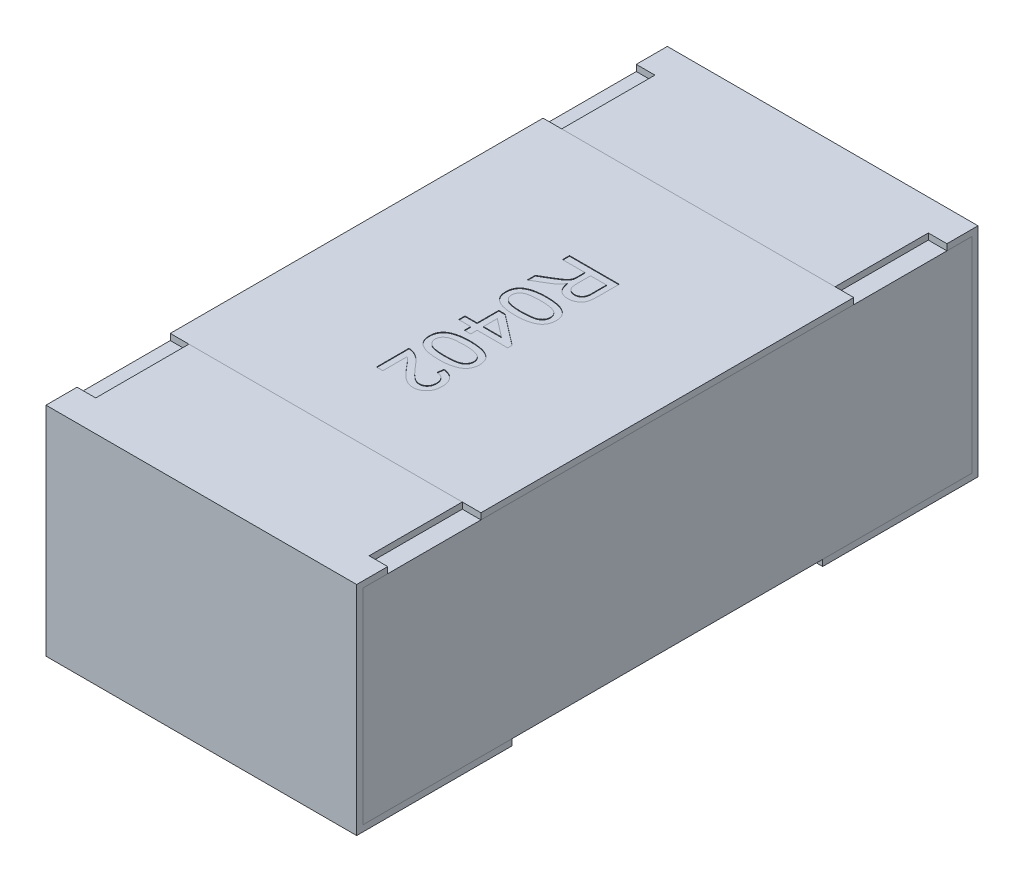
SolidWorks part; units mm, degrees
ref_plane "Front Plane" through (0, 0, 0) normal (0, 0, 1) x (1, 0, 0)
ref_plane "Top Plane" through (0, 0, 0) normal (0, 1, 0) x (1, 0, 0)
ref_plane "Right Plane" through (0, 0, 0) normal (1, 0, 0) x (0, 0, -1)
sketch "Sketch4" plane through (0, 0, 0) normal (1, 0, 0) x (0, 0, -1)
  line L0 (0, 0.1169) -> (0, -0.0721) construction
  line L1 (-0.5, 0) -> (0.3788, 0) construction
  line L2 (-0.5, 0.175) -> (-0.5, -0.175)
  line L3 (-0.5, -0.175) -> (-0.25, -0.175)
  line L4 (-0.3, 0.175) -> (-0.3, 0.165)
  line L5 (-0.3, 0.165) -> (-0.49, 0.165)
  line L6 (-0.49, 0.165) -> (-0.49, -0.165)
  line L7 (-0.49, -0.165) -> (-0.25, -0.165)
  line L8 (-0.25, -0.165) -> (-0.25, -0.175)
  line L9 (-0.3, 0.175) -> (-0.5, 0.175)
  line L10 (0.3, 0.175) -> (0.5, 0.175)
  line L11 (0.25, -0.165) -> (0.25, -0.175)
  line L12 (0.49, -0.165) -> (0.25, -0.165)
  line L13 (0.49, 0.165) -> (0.49, -0.165)
  line L14 (0.3, 0.165) -> (0.49, 0.165)
  line L15 (0.3, 0.175) -> (0.3, 0.165)
  line L16 (0.5, -0.175) -> (0.25, -0.175)
  line L17 (0.5, 0.175) -> (0.5, -0.175)
  dimension "LENGTH" = 0.5
  dimension "HEIGHT" = 0.35
  dimension "END CAP TOP LENGTH" = 0.2
  dimension "END CAP BOTTOM LENGTH" = 0.25
  dimension "D5" = 0.01
  dimension "D6" = 0.01
extrude "Boss-Extrude2" add sketch "Sketch4" along normal mid plane 0.5
sketch "Sketch5" plane through (0, 0, 0) normal (1, 0, 0) x (0, 0, -1)
  line L1 (-0.49, 0.165) -> (0.49, 0.165)
  line L2 (-0.49, 0.165) -> (-0.49, -0.165)
  line L3 (-0.49, -0.165) -> (0.49, -0.165)
  line L4 (0.49, 0.165) -> (0.49, -0.165)
extrude "Boss-Extrude3" add sketch "Sketch5" along normal up to surface and the other way up to surface separate body
sketch "Sketch6" plane through (0, 0.175, 0) normal (0, 1, 0) x (1, 0, 0)
  line L0 (-0.25, 0.5) -> (-0.25, 0.3) construction
  line L1 (-0.25, 0.45) -> (-0.22, 0.45)
  line L2 (-0.25, 0.45) -> (-0.25, 0.3)
  line L3 (-0.25, 0.3) -> (-0.22, 0.3)
  line L4 (-0.22, 0.45) -> (-0.22, 0.3)
  line L5 (0.25, 0.3) -> (-0.25, 0.3) construction
  line L6 (0, 0.0345) -> (0, -0.0345) construction
  line L7 (-0.0325, 0) -> (0.03, 0) construction
  line L8 (0.25, 0.45) -> (0.25, 0.3)
  line L9 (0.25, 0.3) -> (0.22, 0.3)
  line L10 (0.22, 0.45) -> (0.22, 0.3)
  line L11 (0.25, 0.45) -> (0.22, 0.45)
  line L12 (0.25, -0.45) -> (0.22, -0.45)
  line L13 (0.25, -0.45) -> (0.25, -0.3)
  line L14 (0.25, -0.3) -> (0.22, -0.3)
  line L15 (0.22, -0.45) -> (0.22, -0.3)
  line L16 (-0.25, -0.45) -> (-0.22, -0.45)
  line L17 (-0.25, -0.45) -> (-0.25, -0.3)
  line L18 (-0.25, -0.3) -> (-0.22, -0.3)
  line L19 (-0.22, -0.45) -> (-0.22, -0.3)
  dimension "TOP CUT WIDTH" = 0.03
  dimension "TOP CUT LENGTH" = 0.15
extrude "Cut-Extrude1" cut sketch "Sketch6" against normal up to surface (0.01 mm away) up to face at (0, 0.165, 0)
sketch "Sketch7" plane through (0, 0.165, 0) normal (0, 1, 0) x (1, 0, 0)
  line L1 (-0.25, 0.3) -> (0.25, 0.3)
  line L2 (-0.25, 0.3) -> (-0.25, -0.3)
  line L3 (-0.25, -0.3) -> (0.25, -0.3)
  line L4 (0.25, 0.3) -> (0.25, -0.3)
  line L5 (0.22, -0.3) -> (-0.22, -0.3) construction
  line L6 (0.22, 0.3) -> (-0.22, 0.3) construction
  line L7 (-0.25, -0.49) -> (-0.25, 0.49) construction
  line L8 (0.25, 0.49) -> (0.25, -0.49) construction
extrude "Boss-Extrude4" add sketch "Sketch7" along normal up to surface (0.01 mm away) separate body up to face at (0, 0.175, -0.425)
sketch "Sketch9" plane through (0, 0.175, 0) normal (0, 1, 0) x (1, 0, 0)
  line L0 (-0.0372, 0.139) -> (-0.0372, -0.139) construction
  line L1 (-0.0372, 0) -> (0, 0) construction
  text T0 "R0402" font "Arial" height 0.08
extrude "TEXT0402" cut sketch "Sketch9" against normal blind 0.001
